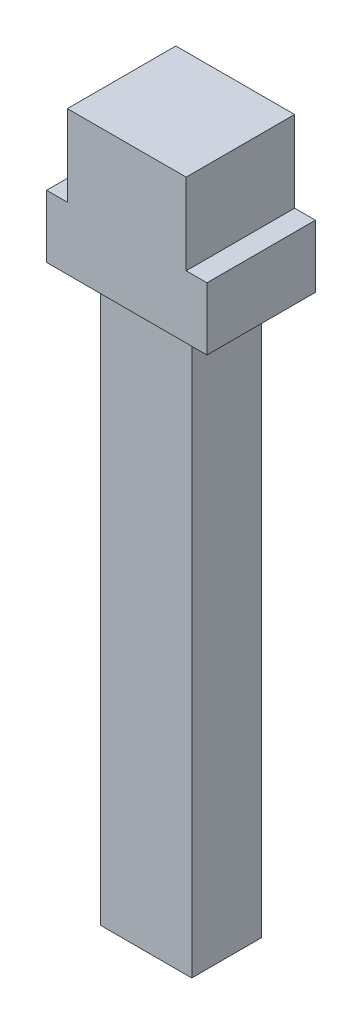
SolidWorks part; units mm, degrees
ref_plane "Front" through (0, 0, 0) normal (0, 0, 1) x (1, 0, 0)
ref_plane "Top" through (0, 0, 0) normal (0, 1, 0) x (1, 0, 0)
ref_plane "Right" through (0, 0, 0) normal (1, 0, 0) x (0, 0, -1)
sketch "Sketch1" plane through (0, 0, 0) normal (0, 0, 1) x (1, 0, 0)
  line L0 (11.5, -2.8617) -> (11.5, 12.8512)
  line L1 (11.5201, -14.9674) -> (15.5201, -14.9674)
  line L2 (-11.5, 12.8315) -> (11.5, 12.8512)
  line L3 (11.5, -2.8617) -> (15.5201, -2.8617)
  line L6 (0, 0) -> (0, -97.1979) construction
  line L7 (-8.8496, -124.623) -> (-8.8496, -14.9674)
  line L8 (-8.8496, -124.623) -> (8.8496, -124.623)
  line L9 (11.5, 35.6991) -> (-11.5, 35.6991) construction
  line L10 (8.8496, -124.623) -> (8.8496, -14.9674)
  line L11 (-8.8496, -124.623) -> (8.8496, -14.9674) construction
  line L12 (-8.8496, -14.9674) -> (8.8496, -124.623) construction
  line L13 (-15.5, -2.8617) -> (-11.5, -2.8617) construction
  line L14 (0, 12.8414) -> (0, 0) construction
  line L15 (-15.5201, -14.9674) -> (-11.5201, -14.9674)
  line L16 (-15.5201, -14.9674) -> (-15.5201, -2.8617)
  line L17 (-15.5201, -2.8617) -> (-11.5, -2.8617)
  line L18 (15.5201, -14.9674) -> (15.5201, -2.8617)
  line L19 (-15.5201, -14.9674) -> (15.5201, -2.8617) construction
  line L20 (-15.5201, -2.8617) -> (15.5201, -14.9674) construction
  line L22 (-11.5201, -14.9674) -> (-8.8496, -14.9674)
  line L23 (8.8496, -14.9674) -> (11.5201, -14.9674)
  line L24 (-11.5, -2.8617) -> (-11.5, 12.8315)
  point P1 (0, 0)
  point P9 (0, -69.7952)
  point P11 (0, -8.9145)
extrude "Boss-Extrude1" add sketch "Sketch1" along normal up to surface (21 mm away)
sketch "Sketch2" plane through (0, -14.9674, 0) normal (0, -1, 0) x (1, 0, 0)
  line L0 (-8.8496, 10.5) -> (-12.1848, 10.5) construction
  line L1 (-15.5201, 0) -> (-8.8496, 0) construction
  line L2 (-8.8496, 0) -> (-8.8496, 21) construction
  line L3 (-8.8496, 21) -> (-8.8496, 0) construction
  line L4 (-12.1848, 10.5) -> (-15.5201, 10.5) construction
  line L5 (0, 0) -> (0, 20) construction
  line L6 (-15.5201, 21) -> (-15.5201, 0) construction
  circle A0 centre (-12.1848, 10.5) radius 2.3327
  circle A1 centre (12.1848, 10.5) radius 2.3327
extrude "Cut-Extrude1" cut sketch "Sketch2" against normal blind 11
sketch "Sketch3" plane through (-8.8496, 0, 0) normal (-1, 0, 0) x (0, 0, 1)
  line L1 (21, -14.9674) -> (17.2657, -14.9674)
  line L2 (21, -14.9674) -> (21, -124.623)
  line L3 (21, -124.623) -> (17.2657, -124.623)
  line L4 (17.2657, -14.9674) -> (17.2657, -124.623)
  line L5 (10.5, -14.9674) -> (10.5, -119.623) construction
  line L6 (21, -14.9674) -> (0, -14.9674) construction
  line L7 (3.7343, -14.9674) -> (3.7343, -124.623)
  line L8 (0, -124.623) -> (3.7343, -124.623)
  line L9 (0, -14.9674) -> (0, -124.623)
  line L10 (0, -14.9674) -> (3.7343, -14.9674)
  line L12 (21, -124.623) -> (0, -124.623) construction
extrude "Cut-Extrude2" cut sketch "Sketch3" against normal up to next
